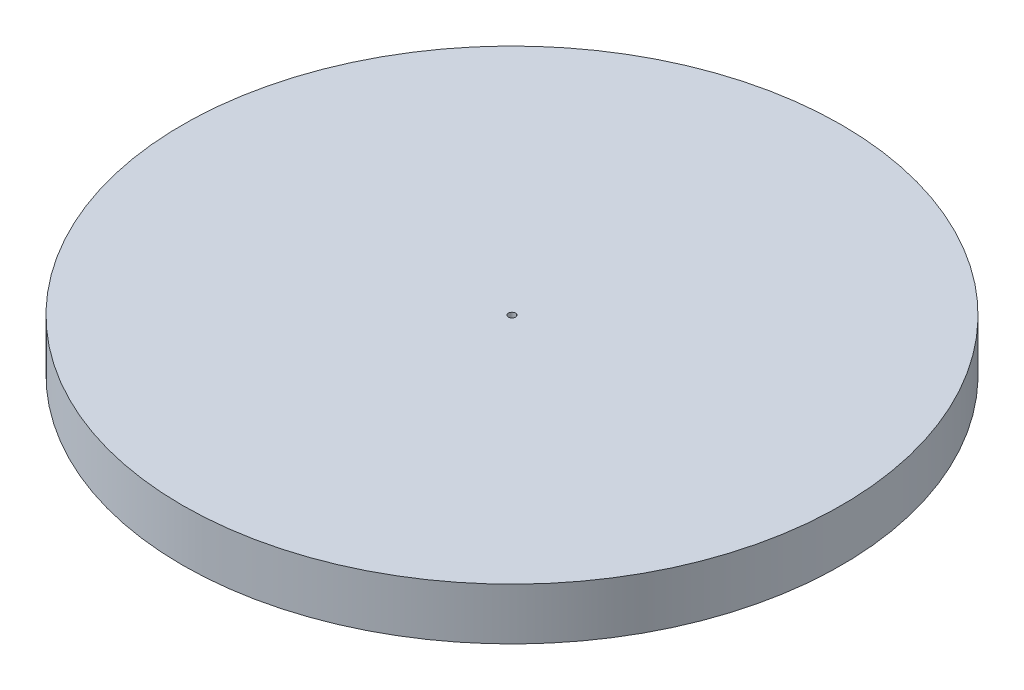
SolidWorks part; units mm, degrees
material "PS Medium/High Flow"
ref_plane "Front Plane" through (0, 0, 0) normal (0, 0, 1) x (1, 0, 0)
ref_plane "Top Plane" through (0, 0, 0) normal (0, 1, 0) x (1, 0, 0)
ref_plane "Right Plane" through (0, 0, 0) normal (1, 0, 0) x (0, 0, -1)
sketch "Sketch1" plane through (0, 0, 0) normal (0, 1, 0) x (1, 0, 0)
  circle A0 centre (0, 0) radius 70
  dimension "D1" = 140
extrude "Boss-Extrude1" add sketch "Sketch1" along normal blind 11
sketch "Sketch3" plane through (0, 11, 0) normal (0, 1, 0) x (1, 0, 0)
  circle A0 centre (0, 0) radius 0.75
  dimension "D1" = 1.5
extrude "Cut-Extrude1" cut sketch "Sketch3" against normal up to next
